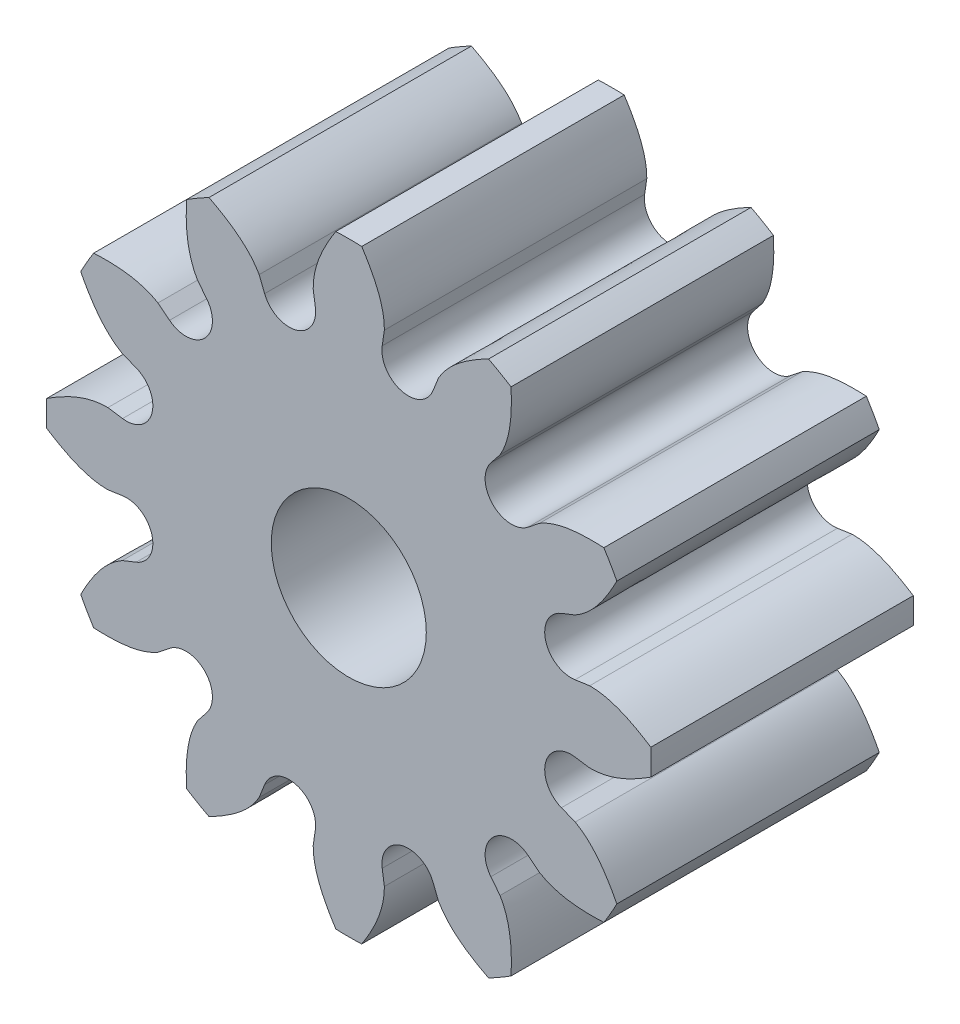
SolidWorks part; units mm, degrees
material "PE Low/Medium Density"
ref_plane "Front Plane" through (0, 0, 0) normal (0, 0, 1) x (1, 0, 0)
ref_plane "Top Plane" through (0, 0, 0) normal (0, 1, 0) x (1, 0, 0)
ref_plane "Right Plane" through (0, 0, 0) normal (1, 0, 0) x (0, 0, -1)
sketch "Involute construction sketch" plane through (0, 0, 0) normal (0, 0, 1) x (1, 0, 0)
  line L0 (0, 0) -> (-1.7439, 2.1811) construction
  line L1 (0, 0) -> (-1.0894, 2.5713) construction
  line L2 (0, 0) -> (-0.3538, 2.7701) construction
  line L3 (0, 0) -> (0.4081, 2.7626) construction
  line L4 (-2.6243, 0.9546) -> (-2.2686, 1.6285) construction
  line L5 (-2.2686, 1.6285) -> (-1.7439, 2.1811) construction
  line L6 (-1.7439, 2.1811) -> (-1.0894, 2.5713) construction
  line L7 (0, 0) -> (-2.2686, 1.6285) construction
  line L8 (0, 0) -> (-2.6243, 0.9546) construction
  line L9 (-1.0894, 2.5713) -> (-0.3538, 2.7701) construction
  line L10 (-0.3538, 2.7701) -> (0.4081, 2.7626) construction
  line L11 (-2.6243, 0.9546) -> (-1.3219, 4.5351) construction
  line L12 (-2.2686, 1.6285) -> (-0.4912, 4.1046) construction
  line L13 (-1.7439, 2.1811) -> (0.0415, 3.6087) construction
  line L14 (-1.0894, 2.5713) -> (0.3138, 3.1658) construction
  line L15 (-0.3538, 2.7701) -> (0.402, 2.8666) construction
  line L17 (0, 0) -> (0, 5.7859) construction
  line L18 (0, 0) -> (0.3879, 2.9464) construction
  line L19 (0, 0) -> (0.6048, 2.2572) construction
  circle A0 centre (0, 0) radius 2.3368 construction
  circle A1 centre (0, 0) radius 2.7926 construction
  circle A2 centre (0, 0) radius 2.9718 construction
  circle A3 centre (0, 0) radius 3.4671 construction
  spline S0 degree 3 poles (0.4081, 2.7626) (0.4101, 2.9021) (0.3192, 3.2075) (-0.15, 3.946) (-0.8068, 4.3472) (-1.3219, 4.5351) knots 0 0 0 0 0.160098 0.360084 1 1 1 1 construction
  point P17 (0.1486, 3.4639)
  dimension "D1" = 4.6736
  dimension "D2" = 5.5852
  dimension "D3" = 5.9436
  dimension "D4" = 6.9342
  dimension "D5" = 0.762
  dimension "D6" = 1.524
  dimension "D7" = 2.286
  dimension "D8" = 3.048
  dimension "D9" = 3.81
  dimension "D10" = 7.5
  dimension "D11" = 15
sketch "Sketch2" plane through (0, 0, 0) normal (0, 0, 1) x (1, 0, 0)
  line L0 (0, 3.4671) -> (0, 2.3368)
  line L1 (0, 0) -> (0, 5.7859) construction
  line L2 (0.4081, 2.7626) -> (0.3833, 2.5944)
  line L3 (0, 0) -> (0.4081, 2.7626) construction
  circle A0 centre (0, 0) radius 3.4671 construction
  circle A1 centre (0, 0) radius 2.3368 construction
  arc A2 (0, 3.4671) -> (0.1486, 3.4639) centre (0, 0) cw
  arc A3 (0, 2.3368) -> (0.6048, 2.2572) centre (0, 0) cw
  arc A4 (0.3833, 2.5944) -> (0.6048, 2.2572) centre (0.6833, 2.5501) ccw
  spline S0 degree 3 poles (0.4081, 2.7626) (0.4091, 2.8245) (0.3774, 3.0766) (0.25, 3.3056) (0.1486, 3.4639) knots 0 0 0 0 0.244448 1 1 1 1
sketch "Sketch3" plane through (0, 0, 0) normal (0, 0, 1) x (1, 0, 0)
  circle A0 centre (0, 0) radius 2.3368
  circle A1 centre (0, 0) radius 0.889
  dimension "D1" = 4.6736
  dimension "D2" = 1.778
extrude "Base" add sketch "Sketch3" along normal blind 3.0099
extrude "Half tooth" add sketch "Sketch2" along normal up to surface (3.0099 mm away) up to face at (2.3368, 0, 3.0099)
ref_plane "Midplane of half tooth" through (0, 0, 0) normal (-1, 0, 0) x (0, 0, 1)
mirror "Mirror of half tooth" about plane through (0, 0, 0) normal (-1, 0, 0) of "Half tooth"
pattern_circular "Pattern of half tooth" count 12 over 360 about axis through (0, 0, 3.0099) along (0, 0, 1) of "Half tooth", "Mirror of half tooth"
equation "\"radtodeg\"= 180 / PI'radian to degree conversion [ ]"
equation "\"phi\"= 20'pressure angle [deg]"
equation "\"N\"= 12'number of teeth [teeth]"
equation "\"A\"= 0.273in'diameter of addendum circle [inch]"
equation "\"B\"= 0.184in'diameter of dedendum circle [inch]"
equation "\"P\"= ( \"N\" + 2 ) / \"A\"'diametral pitch [teeth/inch]"
equation "\"d\"= \"N\" / \"P\"'diameter of pitch circle [inch]"
equation "\"cp\"= PI / \"P\"'circular pitch [inch/teeth]"
equation "\"add\"= 1 / \"P\"'addendum [inch]"
equation "\"ded\"= - ( \"B\" - \"d\" ) / 2'dedendum [inch]"
equation "\"clear\"= \"ded\" - \"add\"'clearance [inch]"
equation "\"C\"= \"B\" + 2 * \"clear\"'diameter of clearance circle [inch]"
equation "\"h\"= \"add\" + \"ded\"'tooth height / whole depth [inch]"
equation "\"s\"= \"d\" * cos ( \"phi\" * 1 / \"radtodeg\" )'diameter of base circle [inch]"
equation "\"t\"= ( PI / 2 ) / \"P\"'tooth width at diameter of pitch circle diameter [inch]"
equation "\"alpha\"= ( \"t\" / ( \"d\" / 2 ) * \"radtodeg\" ) / 2'arc angle for half of tooth width at pitch circle diameter [inch]"
equation "\"bore\"= 0.07'bore of hub [inch]"
equation "\"D4@Involute construction sketch\"= \"A\"'addendum circle"
equation "\"D3@Involute construction sketch\"= \"d\"'pitch circle"
equation "\"D2@Involute construction sketch\"= \"s\"'base circle"
equation "\"D1@Involute construction sketch\"= \"B\"'dedendum circle"
equation "\"seg\"= \"D5@Involute construction sketch\"'size of one involute segment [inch]"
equation "\"D6@Involute construction sketch\"=2*\"seg\""
equation "\"D7@Involute construction sketch\"=3*\"seg\""
equation "\"D8@Involute construction sketch\"=4*\"seg\""
equation "\"D9@Involute construction sketch\"=5*\"seg\""
equation "\"D10@Involute construction sketch\"=\"alpha\""
equation "\"D11@Involute construction sketch\"=2*\"alpha\""
equation "\"D1@Sketch3\"=\"B\""
equation "\"D2@Sketch3\"=\"bore\""
